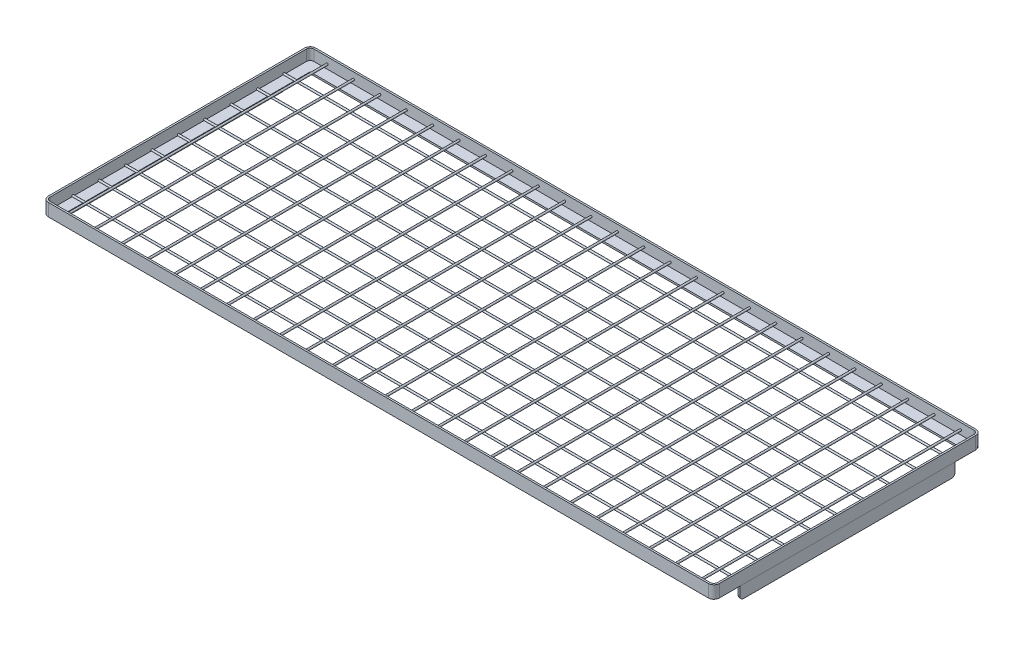
SolidWorks part; units mm, degrees
ref_plane "Front Plane" through (0, 0, 0) normal (0, 0, 1) x (1, 0, 0)
ref_plane "Top Plane" through (0, 0, 0) normal (0, 1, 0) x (1, 0, 0)
ref_plane "Right Plane" through (0, 0, 0) normal (1, 0, 0) x (0, 0, -1)
sketch "Sketch1" plane through (0, 0, 0) normal (0, 1, 0) x (1, 0, 0)
  line L0 (-667.0675, -270.256) -> (667.0675, -270.256)
  line L1 (-667.0675, -266.7) -> (667.0675, -266.7)
  line L2 (-674.6875, -259.08) -> (-674.6875, 259.08)
  line L3 (-667.0675, 266.7) -> (667.0675, 266.7)
  line L4 (674.6875, -259.08) -> (674.6875, 259.08)
  line L5 (678.2435, -259.08) -> (678.2435, 259.08)
  line L6 (-667.0675, 270.256) -> (667.0675, 270.256)
  line L7 (-678.2435, -259.08) -> (-678.2435, 259.08)
  arc A0 (-667.0675, 266.7) -> (-674.6875, 259.08) centre (-667.0675, 259.08) ccw
  arc A1 (-674.6875, -259.08) -> (-667.0675, -266.7) centre (-667.0675, -259.08) ccw
  arc A2 (667.0675, -266.7) -> (674.6875, -259.08) centre (667.0675, -259.08) ccw
  arc A3 (674.6875, 259.08) -> (667.0675, 266.7) centre (667.0675, 259.08) ccw
  arc A4 (667.0675, -270.256) -> (678.2435, -259.08) centre (667.0675, -259.08) ccw
  arc A5 (678.2435, 259.08) -> (667.0675, 270.256) centre (667.0675, 259.08) ccw
  arc A6 (-667.0675, 270.256) -> (-678.2435, 259.08) centre (-667.0675, 259.08) ccw
  arc A7 (-678.2435, -259.08) -> (-667.0675, -270.256) centre (-667.0675, -259.08) ccw
  point P0 (0, 0)
  dimension "D1" = 1349.375
  dimension "D2" = 533.4
  dimension "D3" = 3.556
extrude "Boss-Extrude1" add sketch "Sketch1" along normal blind 21.844
sketch "Sketch3" plane through (0, 0, 0) normal (0, -1, 0) x (1, 0, 0)
  line L0 (652.8435, 244.856) -> (652.8435, -244.856)
  line L1 (-667.0675, 270.256) -> (667.0675, 270.256)
  line L2 (-678.2435, 259.08) -> (-678.2435, -259.08)
  line L3 (-667.0675, -270.256) -> (667.0675, -270.256)
  line L4 (678.2435, 259.08) -> (678.2435, -259.08)
  line L5 (-678.2435, 270.256) -> (678.2435, -270.256) construction
  line L6 (-678.2435, -270.256) -> (673.3657, 268.3123) construction
  line L7 (-652.8435, -244.856) -> (652.8435, -244.856)
  line L8 (-652.8435, 244.856) -> (-652.8435, -244.856)
  line L9 (-652.8435, 244.856) -> (652.8435, 244.856)
  line L10 (-678.2435, 270.256) -> (678.2435, 270.256) construction
  line L11 (678.2435, 270.256) -> (678.2435, -270.256) construction
  line L12 (-678.2435, -270.256) -> (678.2435, -270.256) construction
  line L13 (-678.2435, 270.256) -> (-678.2435, -270.256) construction
  arc A0 (678.2435, 259.08) -> (667.0675, 270.256) centre (667.0675, 259.08) ccw
  arc A1 (667.0675, -270.256) -> (678.2435, -259.08) centre (667.0675, -259.08) ccw
  arc A2 (-678.2435, -259.08) -> (-667.0675, -270.256) centre (-667.0675, -259.08) ccw
  arc A3 (-667.0675, 270.256) -> (-678.2435, 259.08) centre (-667.0675, 259.08) ccw
  point P0 (0, 0)
  dimension "D1" = 25.4
extrude "Boss-Extrude2" add sketch "Sketch3" along normal blind 3.556
sketch "Sketch10" plane through (-674.6875, 0, 0) normal (1, 0, 0) x (0, 0, -1)
  line L1 (-259.08, -3.556) -> (259.08, -3.556) construction
  circle A0 centre (0, 1.524) radius 1.905
  point P4 (137.2015, -1.524)
  point P6 (0, -1.524)
  dimension "D1" = 3.81
  dimension "D2" = 5.08
  dimension "D3" = 259.08
extrude "Boss-Extrude13" add sketch "Sketch10" along normal up to next (1349.375 mm away)
pattern_linear "LPattern1" count 5 spacing 53.34 along (0, 0, 1) count 5 spacing 53.34 along (0, 0, -1) of "Boss-Extrude13"
sketch "Sketch8" plane through (-678.2435, 0, 0) normal (-1, 0, 0) x (0, 0, 1)
  line L0 (-259.08, 21.844) -> (259.08, -3.556) construction
  line L1 (259.08, -3.556) -> (-259.08, -3.556) construction
  line L2 (0, 9.144) -> (0, -113.0774) construction
  line L4 (-217.4875, -28.956) -> (217.4875, -28.956)
  line L5 (-217.4875, -28.956) -> (-217.4875, -3.556)
  line L6 (-217.4875, -3.556) -> (217.4875, -3.556)
  line L7 (217.4875, -28.956) -> (217.4875, -3.556)
  line L8 (-217.4875, -28.956) -> (217.4875, -3.556) construction
  line L9 (-217.4875, -3.556) -> (217.4875, -28.956) construction
  point P8 (0, -16.256)
  dimension "D1" = 434.975
  dimension "D2" = 25.4
extrude "Boss-Extrude11" add sketch "Sketch8" against normal blind 3.556 separate body
sketch "Sketch11" plane through (0, 0, 266.7) normal (0, 0, -1) x (-1, 0, 0)
  line L0 (667.0675, 0) -> (-667.0675, 0) construction
  circle A0 centre (0, 8.89) radius 1.905
  dimension "D1" = 3.81
  dimension "D2" = 8.89
extrude "Boss-Extrude14" add sketch "Sketch11" along normal up to next (533.4 mm away)
pattern_linear "LPattern2" count 13 spacing 53.34 along (-1, 0, 0) count 13 spacing 53.34 along (1, 0, 0) of "Boss-Extrude14"
sketch "Sketch9" plane through (678.2435, 0, 0) normal (1, 0, 0) x (0, 0, -1)
  line L0 (0, -3.556) -> (0, -163.5002) construction
  line L1 (-217.4875, -3.556) -> (217.4875, -3.556) construction
  line L2 (259.08, -3.556) -> (-259.08, -3.556) construction
  line L3 (-217.4875, -28.956) -> (217.4875, -28.956)
  line L4 (-217.4875, -28.956) -> (-217.4875, -3.556)
  line L5 (-217.4875, -3.556) -> (217.4875, -3.556)
  line L6 (217.4875, -28.956) -> (217.4875, -3.556)
  line L7 (-217.4875, -28.956) -> (217.4875, -3.556) construction
  line L8 (-217.4875, -3.556) -> (217.4875, -28.956) construction
  point P5 (0, -16.256)
  dimension "D1" = 25.4
  dimension "D2" = 434.975
extrude "Boss-Extrude12" add sketch "Sketch9" against normal blind 3.556 separate body
fillet "Fillet1" radius 7.62 2 edges at (-676.4655, -28.956, 217.4875) (-676.4655, -28.956, -217.4875)
fillet "Fillet2" radius 7.62 2 edges at (676.4655, -28.956, -217.4875) (676.4655, -28.956, 217.4875)
